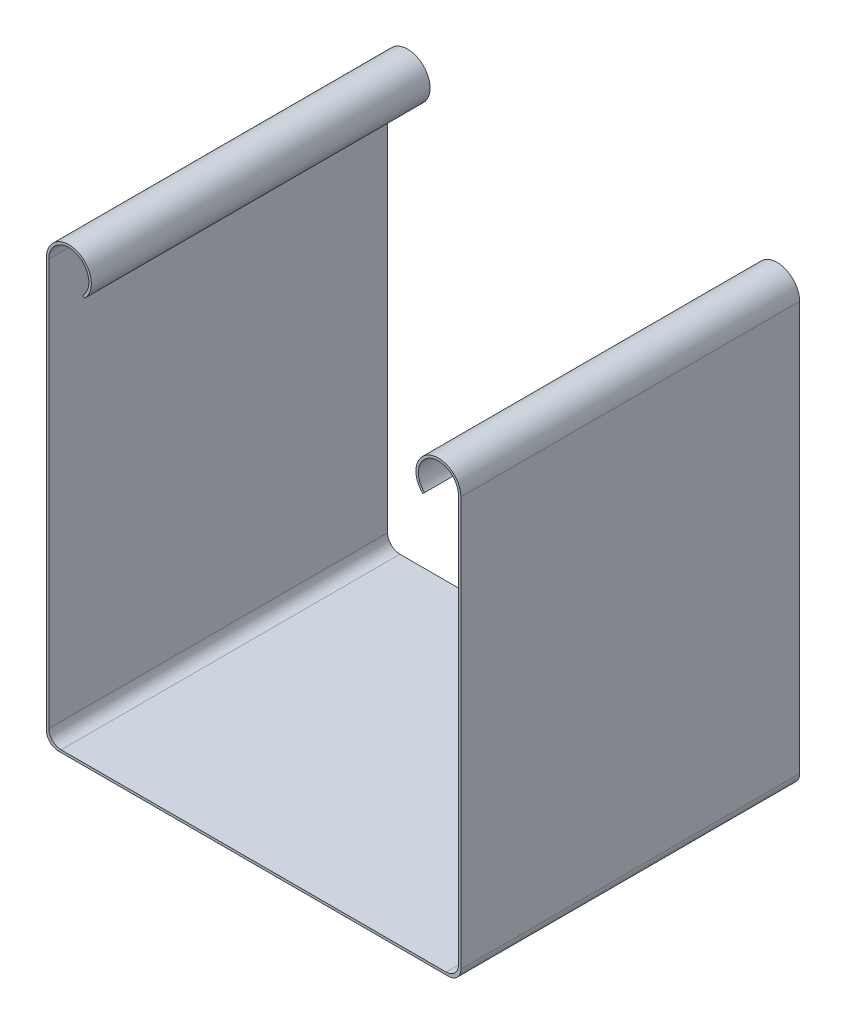
SolidWorks part; units mm, degrees
ref_plane "Plan de face" through (0, 0, 0) normal (0, 0, 1) x (1, 0, 0)
ref_plane "Plan de dessus" through (0, 0, 0) normal (0, 1, 0) x (1, 0, 0)
ref_plane "Plan de droite" through (0, 0, 0) normal (1, 0, 0) x (0, 0, -1)
sketch "Esquisse1" plane through (0, 0, 0) normal (0, 0, 1) x (1, 0, 0)
  line L13 (0, -0.15) -> (0, 72.4519) construction
  line L14 (33.25, 68) -> (33.25, 34)
  line L15 (33.25, 34) -> (33.25, 0)
  line L16 (33.25, 0) -> (0, 0)
  line L17 (33.65, 68) -> (33.65, 34)
  line L18 (33.65, 34) -> (33.65, -0.4)
  line L19 (33.65, -0.4) -> (0, -0.4)
  line L20 (0, -0.4) -> (0, 0)
  line L21 (27.75, 65.6548) -> (27.4671, 65.3719)
  line L22 (33.65, 68) -> (33.65, 34) construction
  arc A0 (33.25, 68) -> (27.75, 65.6548) centre (30, 68) ccw
  circle A3 centre (30, 34) radius 3.25 construction
  arc A7 (33.65, 68) -> (27.4671, 65.3719) centre (30, 68) ccw
  point P9 (27.2313, 65.1361)
  point P13 (30.06, 67.3458)
  point P16 (27.578, 65.4828)
  point P18 (26.75, 68)
  point P19 (0, 0)
  dimension "D14" = 6.5
  dimension "D5" = 3.65
  dimension "D2" = 34
  dimension "D3" = 33.25
  dimension "D4" = 0.4
  dimension "D6" = 45
  dimension "D7" = 1
  dimension "D11" = 34
extrude "Boss.-Extru.2" add sketch "Esquisse1" along normal blind 55
fillet "Congé2" radius 2 2 edges at (33.25, 0, 27.5) (33.65, -0.4, 27.5)
mirror "Symétrie2" about plane through (0, -0.4, 55) normal (1, 0, 0) of bodies 110
